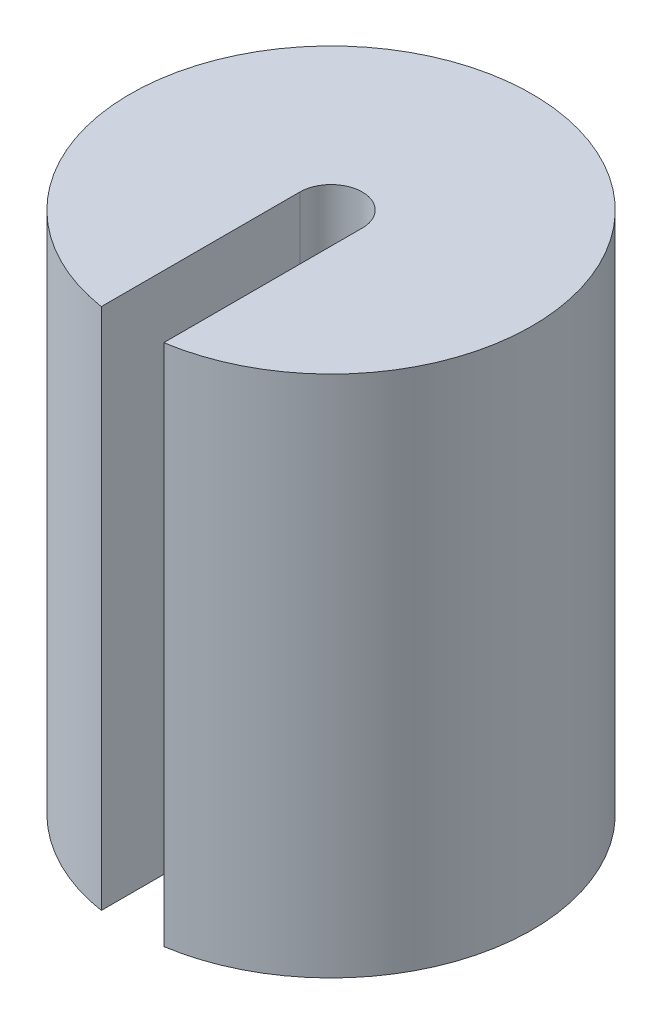
SolidWorks part; units mm, degrees
material "Brass"
ref_plane "Front Plane" through (0, 0, 0) normal (0, 0, 1) x (1, 0, 0)
ref_plane "Top Plane" through (0, 0, 0) normal (0, 1, 0) x (1, 0, 0)
ref_plane "Right Plane" through (0, 0, 0) normal (1, 0, 0) x (0, 0, -1)
sketch "Sketch1" plane through (0, 0, 0) normal (0, 1, 0) x (1, 0, 0)
  circle A0 centre (0, 0) radius 20.75
  dimension "D1" = 41.5
extrude "Boss-Extrude1" add sketch "Sketch1" along normal blind 54
sketch "Sketch2" plane through (0, 54, 0) normal (0, 1, 0) x (1, 0, 0)
  line L0 (-3.225, 0) -> (-3.225, -23.1258)
  line L1 (3.225, 0) -> (3.225, -23.1258)
  line L2 (-3.225, -23.1258) -> (3.225, -23.1258)
  arc A0 (3.225, 0) -> (-3.225, 0) centre (0, 0) ccw
  dimension "D1" = 6.45
  dimension "D2" = 23.1258
extrude "Cut-Extrude1" cut sketch "Sketch2" against normal blind 60.6
